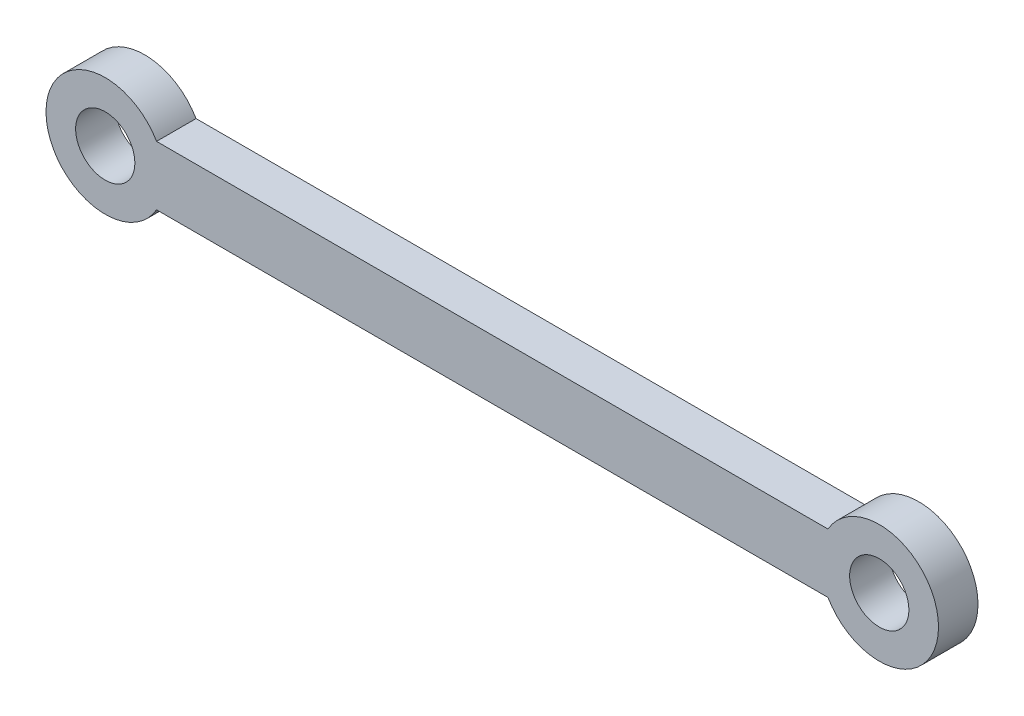
SolidWorks part; units mm, degrees
ref_plane "Front Plane" through (0, 0, 0) normal (0, 0, 1) x (1, 0, 0)
ref_plane "Top Plane" through (0, 0, 0) normal (0, 1, 0) x (1, 0, 0)
ref_plane "Right Plane" through (0, 0, 0) normal (1, 0, 0) x (0, 0, -1)
sketch "Sketch1" plane through (0, 0, 0) normal (0, 0, 1) x (1, 0, 0)
  line L0 (17, -5.4849) -> (17, 15.7585) construction
  line L3 (0, 0) -> (34, 0)
  line L5 (0, 3) -> (34, 3)
  arc A2 (34, 3) -> (34, 0) centre (36.5981, 1.5) cw
  circle A3 centre (36.5981, 1.5) radius 1.5
  arc A4 (0, 0) -> (0, 3) centre (-2.5981, 1.5) cw
  circle A5 centre (-2.5981, 1.5) radius 1.5
  dimension "D3" = 3
  dimension "D4" = 3
  dimension "D5" = 3
  dimension "D6" = 3
  dimension "D1" = 34
  dimension "D2" = 3
extrude "Boss-Extrude1" add sketch "Sketch1" along normal blind 2
